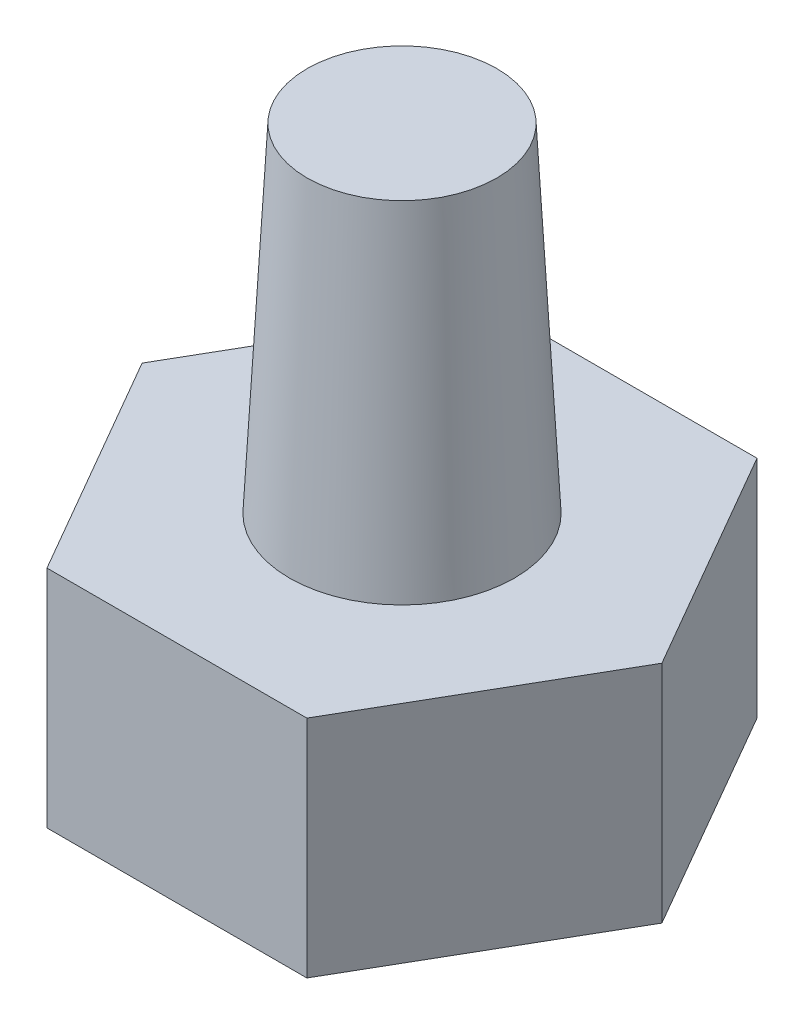
SolidWorks part; units mm, degrees
ref_plane "Front Plane" through (0, 0, 0) normal (0, 0, 1) x (1, 0, 0)
ref_plane "Top Plane" through (0, 0, 0) normal (0, 1, 0) x (1, 0, 0)
ref_plane "Right Plane" through (0, 0, 0) normal (1, 0, 0) x (0, 0, -1)
sketch "Sketch1" plane through (0, 0, 0) normal (0, 1, 0) x (1, 0, 0)
  line L1 (13.8564, 0) -> (6.9282, 12)
  line L2 (6.9282, 12) -> (-6.9282, 12)
  line L3 (-6.9282, 12) -> (-13.8564, 0)
  line L4 (-13.8564, 0) -> (-6.9282, -12)
  line L5 (-6.9282, -12) -> (6.9282, -12)
  line L6 (6.9282, -12) -> (13.8564, 0)
  circle A0 centre (0, 0) radius 12 construction
  dimension "D1" = 24
extrude "Boss-Extrude1" add sketch "Sketch1" along normal blind 12
sketch "Sketch2" plane through (0, 0, 0) normal (0, 1, 0) x (1, 0, 0)
  circle A0 centre (0, 0) radius 6
  dimension "D1" = 12
extrude "Boss-Extrude2" add sketch "Sketch2" along normal blind 18 draft 3 from surface at 12 starting at face at (0, 12, 0)
sketch "Sketch3" plane through (0, 0, 0) normal (0, 1, 0) x (1, 0, 0)
  circle A0 centre (0, 0) radius 10
  dimension "D1" = 20
extrude "Cut-Extrude1" cut sketch "Sketch3" along normal blind 10
